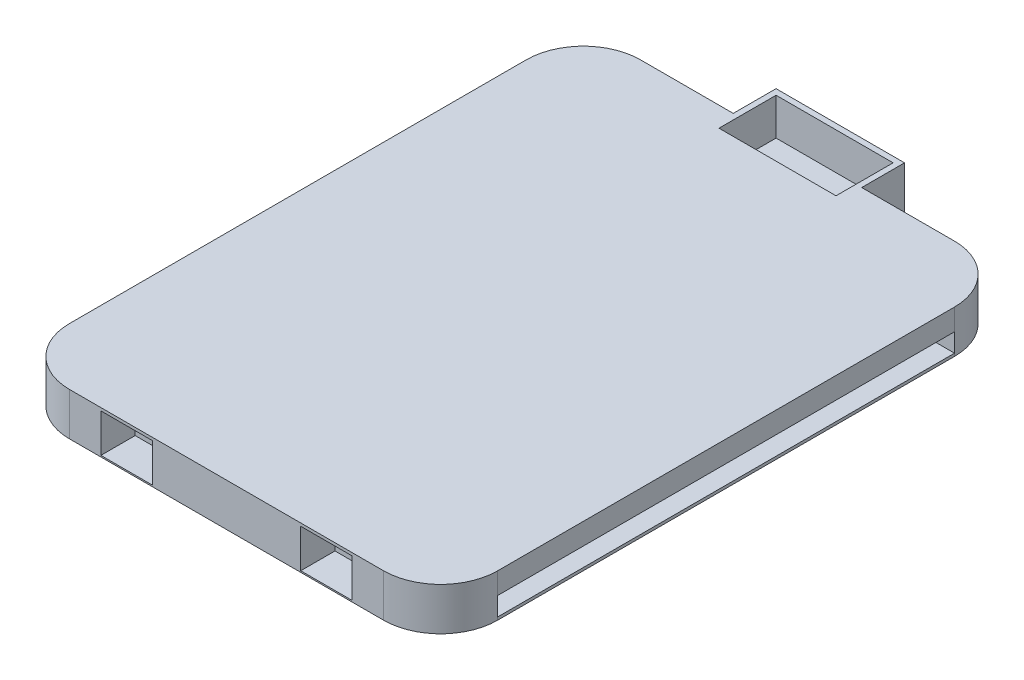
SolidWorks part; units mm, degrees
material "Alloy Steel"
ref_plane "Front Plane" through (0, 0, 0) normal (0, 0, 1) x (1, 0, 0)
ref_plane "Top Plane" through (0, 0, 0) normal (0, 1, 0) x (1, 0, 0)
ref_plane "Right Plane" through (0, 0, 0) normal (1, 0, 0) x (0, 0, -1)
sketch "Sketch1" plane through (0, 0, 0) normal (0, 1, 0) x (1, 0, 0)
  line L0 (-225, 1000) -> (-225, 1150)
  line L1 (-550, 1000) -> (-225, 1000)
  line L2 (-750, 800) -> (-750, -800)
  line L3 (-550, -1000) -> (550, -1000)
  line L4 (750, 800) -> (750, -800)
  line L5 (-750, 1000) -> (750, -1000) construction
  line L6 (-750, -1000) -> (750, 1000) construction
  line L7 (-225, 1150) -> (225, 1150)
  line L8 (225, 1150) -> (225, 1000)
  line L9 (225, 1000) -> (550, 1000)
  arc A0 (-750, -800) -> (-550, -1000) centre (-550, -800) ccw
  arc A1 (550, -1000) -> (750, -800) centre (550, -800) ccw
  arc A2 (-750, 800) -> (-550, 1000) centre (-550, 800) cw
  arc A3 (550, 1000) -> (750, 800) centre (550, 800) cw
  point P0 (0, 0)
  point P20 (0, -1000)
  point P23 (0, 1150)
  dimension "D3" = 200
  dimension "D1" = 1500
  dimension "D2" = 2000
  dimension "D4" = 450
  dimension "D5" = 150
extrude "Boss-Extrude1" add sketch "Sketch1" along normal blind 150
sketch "Sketch2" plane through (750, 0, 0) normal (1, 0, 0) x (0, 0, -1)
  line L0 (-800, 0) -> (800, 0) construction
  line L1 (-200, 75) -> (200, 75)
  line L2 (-200, 75) -> (-200, 10)
  line L3 (-200, 10) -> (200, 10)
  line L4 (200, 75) -> (200, 10)
  line L5 (-200, 75) -> (200, 10) construction
  line L6 (-200, 10) -> (200, 75) construction
  point P0 (0, 42.5)
  dimension "D1" = 400
  dimension "D2" = 65
  dimension "D3" = 10
extrude "Cut-Extrude1" cut sketch "Sketch2" against normal through all both and the other way through all
sketch "Sketch3" plane through (750, 0, 0) normal (1, 0, 0) x (0, 0, -1)
  line L1 (200, 10) -> (800, 10)
  line L2 (200, 10) -> (200, 75)
  line L3 (200, 75) -> (800, 75)
  line L4 (800, 10) -> (800, 75)
  line L5 (-200, 10) -> (-800, 10)
  line L6 (-200, 10) -> (-200, 75)
  line L7 (-200, 75) -> (-800, 75)
  line L8 (-800, 10) -> (-800, 75)
  dimension "D1" = 600
extrude "Cut-Extrude2" cut sketch "Sketch3" against normal blind 130
mirror "Mirror1" about plane through (0, 0, 0) normal (1, 0, 0) of "Cut-Extrude2"
sketch "Sketch4" plane through (0, 150, 0) normal (0, 1, 0) x (1, 0, 0)
  line L0 (-670, 100) -> (-670, -100) construction
  line L1 (-750, 800) -> (-750, -800) construction
  line L2 (750, 0) -> (-750, 0) construction
  line L3 (750, -800) -> (750, 800) construction
  circle A0 centre (-670, 100) radius 5
  circle A1 centre (-670, -100) radius 5
  point P8 (-670, 0)
  dimension "D3" = 10
  dimension "D1" = 200
  dimension "D2" = 80
extrude "Boss-Extrude2" add sketch "Sketch4" against normal blind 150
mirror "Mirror2" about plane through (0, 0, 0) normal (1, 0, 0) of "Boss-Extrude2"
sketch "Sketch5" plane through (0, 0, 1000) normal (0, 0, 1) x (1, 0, 0)
  line L0 (-550, 150) -> (-550, 0) construction
  line L1 (-395, 110) -> (-305, 110)
  line L2 (-395, 110) -> (-395, 35)
  line L3 (-395, 35) -> (-305, 35)
  line L4 (-305, 110) -> (-305, 35)
  line L5 (-395, 110) -> (-305, 35) construction
  line L6 (-395, 35) -> (-305, 110) construction
  line L7 (305, 110) -> (395, 110)
  line L8 (305, 110) -> (305, 35)
  line L9 (305, 35) -> (395, 35)
  line L10 (395, 110) -> (395, 35)
  line L11 (305, 110) -> (395, 35) construction
  line L12 (305, 35) -> (395, 110) construction
  line L14 (550, 150) -> (550, 0) construction
  line L15 (-550, 150) -> (550, 150) construction
  point P0 (-350, 72.5)
  point P5 (350, 72.5)
  dimension "D1" = 75
  dimension "D2" = 90
  dimension "D3" = 200
  dimension "D4" = 200
  dimension "D5" = 40
extrude "Cut-Extrude3" cut sketch "Sketch5" against normal blind 200
sketch "Sketch6" plane through (0, 0, -1150) normal (0, 0, -1) x (-1, 0, 0)
  line L1 (225, 150) -> (225, 0) construction
  circle A0 centre (0, 75) radius 15
  point P8 (225, 75)
  dimension "D1" = 30
extrude "Cut-Extrude4" cut sketch "Sketch6" against normal blind 5
sketch "Sketch7" plane through (0, 0, 1000) normal (0, 0, 1) x (1, 0, 0)
  line L0 (0, 208.079) -> (0, -102.7043) construction
  line L1 (-440, 140) -> (-260, 140)
  line L2 (-440, 140) -> (-440, 5)
  line L3 (-440, 5) -> (-260, 5)
  line L4 (-260, 140) -> (-260, 5)
  line L5 (-440, 140) -> (-260, 5) construction
  line L6 (-440, 5) -> (-260, 140) construction
  line L7 (260, 140) -> (260, 5)
  line L8 (440, 5) -> (260, 5)
  line L9 (440, 140) -> (440, 5)
  line L10 (440, 140) -> (260, 140)
  point P0 (-350, 72.5)
  dimension "D1" = 180
  dimension "D2" = 135
extrude "Cut-Extrude5" cut sketch "Sketch7" against normal blind 120
sketch "Sketch8" plane through (0, 0, -1150) normal (0, 0, -1) x (-1, 0, 0)
  line L0 (-205, 20) -> (205, 20)
  line L1 (205, 20) -> (205, 130)
  line L2 (205, 130) -> (-205, 130)
  line L3 (-205, 130) -> (-205, 20)
  circle A0 centre (0, 75) radius 15 construction
  circle A1 centre (0, 75) radius 15
extrude "Cut-Extrude6" cut sketch "Sketch8" against normal blind 200 from offset 20 offset against normal yes
sketch "Sketch9" plane through (0, 150, 0) normal (0, 1, 0) x (1, 0, 0)
  line L0 (225, 1150) -> (-225, 1150) construction
  line L1 (205, 1130) -> (-205, 1130)
  line L2 (205, 1130) -> (205, 930)
  line L3 (205, 930) -> (-205, 930)
  line L4 (-205, 1130) -> (-205, 930)
  line L5 (205, 1130) -> (-205, 930) construction
  line L6 (205, 930) -> (-205, 1130) construction
  line L7 (-225, 1150) -> (-225, 1000) construction
  point P0 (0, 1030)
  dimension "D1" = 20
  dimension "D2" = 20
  dimension "D3" = 200
extrude "Cut-Extrude7" cut sketch "Sketch9" against normal blind 127
